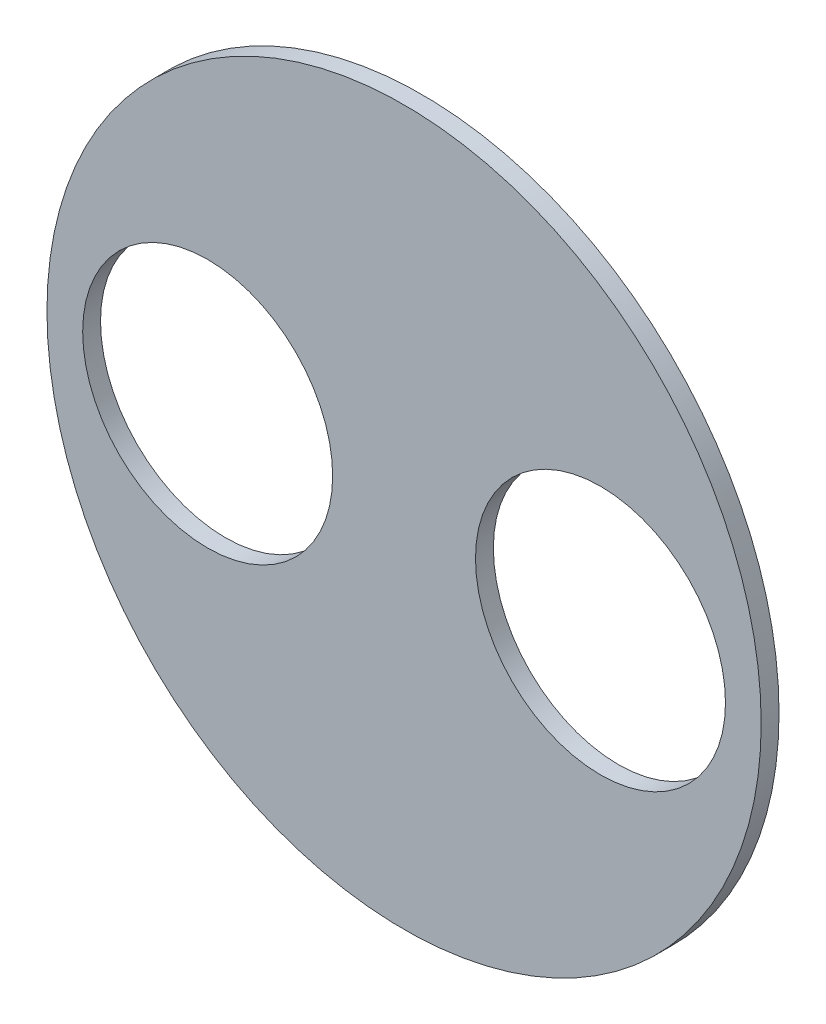
SolidWorks part; units mm, degrees
ref_plane "Front Plane" through (0, 0, 0) normal (0, 0, 1) x (1, 0, 0)
ref_plane "Top Plane" through (0, 0, 0) normal (0, 1, 0) x (1, 0, 0)
ref_plane "Right Plane" through (0, 0, 0) normal (1, 0, 0) x (0, 0, -1)
sketch "Sketch1" plane through (0, 0, 0) normal (0, 0, 1) x (1, 0, 0)
  line L0 (0, 34.925) -> (0, -34.925) construction
  line L1 (34.925, 0) -> (-34.925, 0) construction
  circle A0 centre (0, 0) radius 63.5
  circle A1 centre (34.925, 0) radius 22.225
  circle A2 centre (0, 34.925) radius 22.225 construction
  circle A3 centre (-34.925, 0) radius 22.225
  circle A4 centre (0, -34.925) radius 22.225 construction
  dimension "D1" = 127
  dimension "D2" = 44.45
  dimension "D3" = 69.85
extrude "Boss-Extrude1" add sketch "Sketch1" along normal blind 3.175
